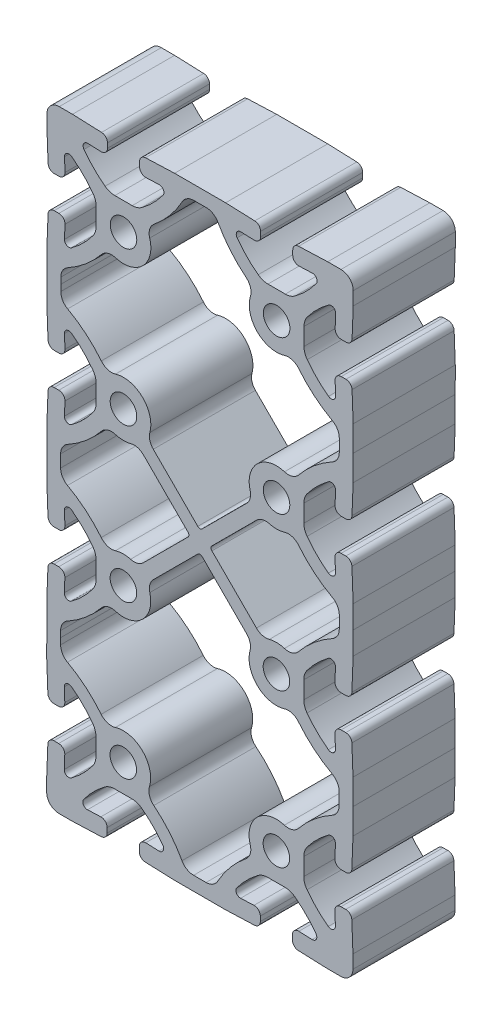
SolidWorks part; units mm, degrees
material "6061 Alloy"
ref_plane "Front" through (0, 0, 0) normal (0, 0, 1) x (1, 0, 0)
ref_plane "Top" through (0, 0, 0) normal (0, 1, 0) x (1, 0, 0)
ref_plane "Right" through (0, 0, 0) normal (1, 0, 0) x (0, 0, -1)
sketch "Sketch1" plane through (0, 0, 0) normal (0, 0, 1) x (1, 0, 0)
  line L0 (29.1885, -14.6975) -> (32.5093, -14.5704)
  line L1 (34.0916, -16.094) -> (34.0911, -17.2633)
  line L2 (32.6254, -18.7854) -> (25.3907, -19.0624)
  line L3 (25.3907, -19.0624) -> (19.0407, -19.0593)
  line L4 (38.0967, -6.8258) -> (35.9379, -6.8248)
  line L5 (19.0407, -19.0593) -> (12.6907, -19.0562)
  line L6 (40.2554, -6.8269) -> (38.0967, -6.8258)
  line L7 (12.6907, -19.0562) -> (5.4563, -18.7721)
  line L8 (3.9921, -17.2486) -> (3.9926, -16.0793)
  line L9 (43.6764, -14.5758) -> (46.9971, -14.7062)
  line L10 (5.5764, -14.5572) -> (8.8971, -14.6876)
  line L11 (42.0921, -17.2672) -> (42.0926, -16.0979)
  line L12 (50.7907, -19.0748) -> (43.5563, -18.7907)
  line L13 (2.1554, -6.8083) -> (-0.0033, -6.8072)
  line L14 (54.0927, -19.0764) -> (50.7907, -19.0748)
  line L15 (-0.0033, -6.8072) -> (-2.1621, -6.8061)
  line L16 (57.1438, -12.7279) -> (57.1422, -16.0299)
  line L17 (56.8668, -5.4932) -> (57.1438, -12.7279)
  line L18 (-8.9115, -14.6789) -> (-5.5907, -14.5517)
  line L19 (54.1754, -4.027) -> (55.3446, -4.0275)
  line L20 (-4.0084, -16.0754) -> (-4.0089, -17.2446)
  line L21 (52.7789, -8.9301) -> (52.6517, -5.6093)
  line L22 (-5.4746, -18.7668) -> (-12.7093, -19.0438)
  line L23 (-12.7093, -19.0438) -> (-16.0113, -19.0422)
  line L24 (44.9072, -0.0219) -> (44.9061, -2.1807)
  line L25 (-19.0578, -15.9927) -> (-19.0562, -12.6907)
  line L26 (44.9082, 2.1368) -> (44.9072, -0.0219)
  line L27 (-19.0562, -12.6907) -> (-18.7721, -5.4563)
  line L28 (-17.2486, -3.9921) -> (-16.0793, -3.9926)
  line L29 (52.6572, 5.5578) -> (52.7876, 8.8785)
  line L30 (-14.5572, -5.5764) -> (-14.6876, -8.8971)
  line L31 (55.3485, 3.9735) -> (54.1793, 3.974)
  line L32 (57.1562, 12.6721) -> (56.8721, 5.4377)
  line L33 (-6.8083, -2.1554) -> (-6.8072, 0.0033)
  line L34 (57.1593, 19.0229) -> (57.1562, 12.6721)
  line L35 (-6.8072, 0.0033) -> (-6.8061, 2.1621)
  line L36 (57.1593, 25.3738) -> (57.1593, 19.0229)
  line L37 (56.8788, 32.6083) -> (57.1593, 25.3738)
  line L38 (54.1866, 34.0733) -> (55.3559, 34.0733)
  line L39 (-14.6789, 8.9115) -> (-14.5517, 5.5907)
  line L40 (52.7925, 29.1694) -> (52.6638, 32.4902)
  line L41 (-16.0754, 4.0084) -> (-17.2446, 4.0089)
  line L42 (-18.7668, 5.4746) -> (-19.0438, 12.7093)
  line L43 (-19.0438, 12.7093) -> (-19.0407, 19.0602)
  line L44 (44.9165, 38.0738) -> (44.9165, 35.915)
  line L45 (-19.0407, 19.0602) -> (-19.0345, 25.411)
  line L46 (44.9165, 40.2325) -> (44.9165, 38.0738)
  line L47 (-19.0345, 25.411) -> (-18.7469, 32.6453)
  line L48 (-17.2226, 34.1087) -> (-16.0533, 34.1076)
  line L49 (52.6638, 43.6573) -> (52.7925, 46.9781)
  line L50 (-14.532, 32.523) -> (-14.664, 29.2024)
  line L51 (55.3559, 42.0743) -> (54.1866, 42.0743)
  line L52 (57.1855, 51.4485) -> (56.8788, 43.5392)
  line L53 (-6.7814, 35.9403) -> (-6.7793, 38.099)
  line L54 (57.1965, 57.1006) -> (57.1855, 51.4485)
  line L55 (-6.7793, 38.099) -> (-6.7772, 40.2578)
  line L56 (57.191, 62.7528) -> (57.1965, 57.1006)
  line L57 (56.892, 70.6624) -> (57.191, 62.7528)
  line L58 (54.2013, 72.1299) -> (55.3706, 72.1288)
  line L59 (-14.6466, 47.011) -> (-14.5211, 43.6901)
  line L60 (52.8024, 67.2275) -> (52.6769, 70.5484)
  line L61 (-16.0455, 42.1086) -> (-17.2148, 42.1097)
  line L62 (-18.7362, 43.5762) -> (-19.0352, 51.4858)
  line L63 (-19.0352, 51.4858) -> (-19.0407, 57.1379)
  line L64 (44.9351, 76.1395) -> (44.933, 73.9807)
  line L65 (-19.0407, 57.1379) -> (-19.0296, 62.79)
  line L66 (44.9372, 78.2983) -> (44.9351, 76.1395)
  line L67 (-19.0296, 62.79) -> (-18.7229, 70.6993)
  line L68 (-17.2001, 72.1643) -> (-16.0308, 72.1643)
  line L69 (52.6878, 81.7155) -> (52.8198, 85.0361)
  line L70 (-14.5079, 70.5812) -> (-14.6367, 67.2605)
  line L71 (55.3784, 80.1298) -> (54.2091, 80.1309)
  line L72 (57.1903, 88.8275) -> (56.9027, 81.5933)
  line L73 (-6.7607, 74.006) -> (-6.7607, 76.1648)
  line L74 (57.1965, 95.1784) -> (57.1903, 88.8275)
  line L75 (-6.7607, 76.1648) -> (-6.7607, 78.3235)
  line L76 (57.1996, 101.5292) -> (57.1965, 95.1784)
  line L77 (56.9226, 108.7639) -> (57.1996, 101.5292)
  line L78 (54.2312, 110.2302) -> (55.4005, 110.2296)
  line L79 (-14.6367, 85.0691) -> (-14.5079, 81.7483)
  line L80 (52.8347, 105.327) -> (52.7076, 108.6479)
  line L81 (-16.0308, 80.1653) -> (-17.2001, 80.1653)
  line L82 (-18.7229, 81.6302) -> (-19.0035, 88.8648)
  line L83 (-19.0035, 88.8648) -> (-19.0035, 95.2156)
  line L84 (44.963, 114.2352) -> (44.962, 112.0764)
  line L85 (-19.0035, 95.2156) -> (-19.0004, 101.5665)
  line L86 (44.9641, 116.394) -> (44.963, 114.2352)
  line L87 (-19.0004, 101.5665) -> (-18.7163, 108.8009)
  line L88 (-17.1927, 110.2651) -> (-16.0234, 110.2645)
  line L89 (52.713, 119.815) -> (52.8434, 123.1357)
  line L90 (-14.5014, 108.6807) -> (-14.6318, 105.36)
  line L91 (55.4044, 118.2306) -> (54.2351, 118.2312)
  line L92 (57.212, 126.9292) -> (56.928, 119.6948)
  line L93 (-6.7524, 112.1017) -> (-6.7514, 114.2605)
  line L94 (57.2136, 130.2312) -> (57.212, 126.9292)
  line L95 (-6.7514, 114.2605) -> (-6.7503, 116.4192)
  line L96 (50.8651, 133.2823) -> (54.1671, 133.2807)
  line L97 (43.6304, 133.0053) -> (50.8651, 133.2823)
  line L98 (-14.6231, 123.1686) -> (-14.4959, 119.8478)
  line L99 (42.1642, 130.3139) -> (42.1648, 131.4832)
  line L100 (-16.0195, 118.2655) -> (-17.1888, 118.2661)
  line L101 (47.0673, 128.9174) -> (43.7465, 128.7903)
  line L102 (-18.711, 119.7318) -> (-18.988, 126.9665)
  line L103 (-18.988, 126.9665) -> (-18.9863, 130.2685)
  line L104 (38.1592, 121.0457) -> (40.3179, 121.0447)
  line L105 (-15.9369, 133.315) -> (-12.6349, 133.3133)
  line L106 (36.0004, 121.0468) -> (38.1592, 121.0457)
  line L107 (-12.6349, 133.3133) -> (-5.4004, 133.0293)
  line L108 (-3.9362, 131.5057) -> (-3.9368, 130.3364)
  line L109 (32.5794, 128.7957) -> (29.2587, 128.9261)
  line L110 (-5.5206, 128.8143) -> (-8.8413, 128.9447)
  line L111 (34.1638, 131.4871) -> (34.1632, 130.3178)
  line L112 (25.4651, 133.2947) -> (32.6996, 133.0107)
  line L113 (-2.0996, 121.0654) -> (0.0592, 121.0643)
  line L114 (19.1151, 133.2978) -> (25.4651, 133.2947)
  line L115 (0.0592, 121.0643) -> (2.2179, 121.0633)
  line L116 (12.7651, 133.3009) -> (19.1151, 133.2978)
  line L117 (5.5304, 133.0239) -> (12.7651, 133.3009)
  line L118 (4.0642, 130.3325) -> (4.0648, 131.5018)
  line L119 (8.9673, 128.936) -> (5.6465, 128.8089)
  line L120 (19.6152, 54.138) -> (30.6889, 43.0561)
  line L121 (7.4532, 43.0675) -> (18.5377, 54.1386)
  line L122 (53.7049, 19.0238) -> (53.7049, 20.5701)
  line L123 (53.7049, 19.0238) -> (53.7041, 17.4774)
  line L124 (-15.5863, 19.0576) -> (-15.5848, 20.604)
  line L125 (-15.5863, 19.0576) -> (-15.587, 17.5113)
  line L126 (19.0424, -15.6049) -> (20.5887, -15.6057)
  line L127 (19.0424, -15.6049) -> (17.496, -15.6042)
  line L128 (19.1135, 129.8434) -> (20.6598, 129.8427)
  line L129 (19.1135, 129.8434) -> (17.5671, 129.8442)
  line L130 (53.7421, 95.1809) -> (53.7429, 96.7273)
  line L131 (53.7421, 95.1809) -> (53.7406, 93.6346)
  line L132 (-15.5491, 95.2148) -> (-15.5483, 96.7611)
  line L133 (-15.5491, 95.2148) -> (-15.5491, 93.6684)
  line L134 (19.6181, 60.1) -> (30.7026, 71.171)
  line L135 (7.4669, 71.1824) -> (18.5406, 60.1005)
  line L136 (53.7451, 58.6323) -> (53.7391, 55.5602)
  line L137 (22.0596, 56.5789) -> (33.1324, 45.4978)
  line L138 (22.0601, 57.6567) -> (33.1438, 68.7269)
  line L139 (5.012, 45.5116) -> (16.0957, 56.5818)
  line L140 (5.0234, 68.7407) -> (16.0963, 57.6596)
  line L141 (-15.5893, 55.6062) -> (-15.5833, 58.6783)
  arc A0 (34.0916, -16.094) -> (32.5093, -14.5704) centre (32.5676, -16.0932) ccw
  arc A1 (28.2492, -12.9315) -> (29.1885, -14.6975) centre (29.146, -13.5873) ccw
  arc A2 (32.6254, -18.7854) -> (34.0911, -17.2633) centre (32.5671, -17.2625) ccw
  arc A3 (33.511, -7.6275) -> (28.2492, -12.9315) centre (48.4243, -27.6843) ccw
  arc A4 (35.9379, -6.8248) -> (33.511, -7.6275) centre (35.9359, -10.8888) ccw
  arc A5 (42.6816, -7.632) -> (40.2554, -6.8269) centre (40.2535, -10.8909) ccw
  arc A6 (3.9921, -17.2486) -> (5.4563, -18.7721) centre (5.5161, -17.2493) ccw
  arc A7 (47.9382, -12.9411) -> (42.6816, -7.632) centre (27.7487, -27.6742) ccw
  arc A8 (46.9971, -14.7062) -> (47.9382, -12.9411) centre (47.0407, -13.596) ccw
  arc A9 (5.5764, -14.5572) -> (3.9926, -16.0793) centre (5.5166, -16.08) ccw
  arc A10 (43.6764, -14.5758) -> (42.0926, -16.0979) centre (43.6166, -16.0986) ccw
  arc A11 (8.8971, -14.6876) -> (9.8382, -12.9225) centre (8.9407, -13.5774) ccw
  arc A12 (9.8382, -12.9225) -> (4.5816, -7.6134) centre (-10.3513, -27.6555) ccw
  arc A13 (42.0921, -17.2672) -> (43.5563, -18.7907) centre (43.6161, -17.2679) ccw
  arc A14 (4.5816, -7.6134) -> (2.1554, -6.8083) centre (2.1535, -10.8723) ccw
  arc A15 (54.0927, -19.0764) -> (57.1422, -16.0299) centre (54.0942, -16.0284) ccw
  arc A16 (-2.1621, -6.8061) -> (-4.589, -7.6089) centre (-2.1641, -10.8701) ccw
  arc A17 (-4.589, -7.6089) -> (-9.8508, -12.9129) centre (10.3243, -27.6656) ccw
  arc A18 (-9.8508, -12.9129) -> (-8.9115, -14.6789) centre (-8.954, -13.5687) ccw
  arc A19 (56.8668, -5.4932) -> (55.3446, -4.0275) centre (55.3439, -5.5515) ccw
  arc A20 (-4.0084, -16.0754) -> (-5.5907, -14.5517) centre (-5.5324, -16.0746) ccw
  arc A21 (54.1754, -4.027) -> (52.6517, -5.6093) centre (54.1746, -5.551) ccw
  arc A22 (-5.4746, -18.7668) -> (-4.0089, -17.2446) centre (-5.5329, -17.2439) ccw
  arc A23 (51.0129, -9.8695) -> (52.7789, -8.9301) centre (51.6687, -8.9726) ccw
  arc A24 (45.7089, -4.6076) -> (51.0129, -9.8695) centre (65.7656, 10.3057) ccw
  arc A25 (44.9061, -2.1807) -> (45.7089, -4.6076) centre (48.9701, -2.1827) ccw
  arc A26 (-19.0578, -15.9927) -> (-16.0113, -19.0422) centre (-16.0098, -15.9942) ccw
  arc A27 (45.7134, 4.5629) -> (44.9082, 2.1368) centre (48.9722, 2.1348) ccw
  arc A28 (-17.2486, -3.9921) -> (-18.7721, -5.4563) centre (-17.2493, -5.5161) ccw
  arc A29 (51.0225, 9.8196) -> (45.7134, 4.5629) centre (65.7555, -10.3699) ccw
  arc A30 (52.7876, 8.8785) -> (51.0225, 9.8196) centre (51.6774, 8.9221) ccw
  arc A31 (-14.5572, -5.5764) -> (-16.0793, -3.9926) centre (-16.08, -5.5166) ccw
  arc A32 (52.6572, 5.5578) -> (54.1793, 3.974) centre (54.18, 5.498) ccw
  arc A33 (-14.6876, -8.8971) -> (-12.9225, -9.8382) centre (-13.5774, -8.9407) ccw
  arc A34 (-12.9225, -9.8382) -> (-7.6134, -4.5816) centre (-27.6555, 10.3513) ccw
  arc A35 (55.3485, 3.9735) -> (56.8721, 5.4377) centre (55.3493, 5.4975) ccw
  arc A36 (-7.6134, -4.5816) -> (-6.8083, -2.1554) centre (-10.8723, -2.1535) ccw
  arc A37 (-6.8061, 2.1621) -> (-7.6089, 4.589) centre (-10.8701, 2.1641) ccw
  arc A38 (-7.6089, 4.589) -> (-12.9129, 9.8508) centre (-27.6656, -10.3243) ccw
  arc A39 (56.8788, 32.6083) -> (55.3559, 34.0733) centre (55.3559, 32.5493) ccw
  arc A40 (-12.9129, 9.8508) -> (-14.6789, 8.9115) centre (-13.5687, 8.954) ccw
  arc A41 (54.1866, 34.0733) -> (52.6638, 32.4902) centre (54.1866, 32.5493) ccw
  arc A42 (-16.0754, 4.0084) -> (-14.5517, 5.5907) centre (-16.0746, 5.5324) ccw
  arc A43 (51.027, 28.2292) -> (52.7925, 29.1694) centre (51.6823, 29.1264) ccw
  arc A44 (-18.7668, 5.4746) -> (-17.2446, 4.0089) centre (-17.2439, 5.5329) ccw
  arc A45 (45.7204, 33.4885) -> (51.027, 28.2292) centre (65.7699, 48.4116) ccw
  arc A46 (44.9165, 35.915) -> (45.7204, 33.4885) centre (48.9805, 35.915) ccw
  arc A47 (45.7204, 42.659) -> (44.9165, 40.2325) centre (48.9805, 40.2325) ccw
  arc A48 (-17.2226, 34.1087) -> (-18.7469, 32.6453) centre (-17.2241, 32.5847) ccw
  arc A49 (51.027, 47.9183) -> (45.7204, 42.659) centre (65.7699, 27.736) ccw
  arc A50 (52.7925, 46.9781) -> (51.027, 47.9183) centre (51.6823, 47.0211) ccw
  arc A51 (-14.532, 32.523) -> (-16.0533, 34.1076) centre (-16.0548, 32.5836) ccw
  arc A52 (52.6638, 43.6573) -> (54.1866, 42.0743) centre (54.1866, 43.5983) ccw
  arc A53 (-14.664, 29.2024) -> (-12.8994, 28.2605) centre (-13.5539, 29.1583) ccw
  arc A54 (-12.8994, 28.2605) -> (-7.5877, 33.5145) centre (-27.6226, 48.4572) ccw
  arc A55 (55.3559, 42.0743) -> (56.8788, 43.5392) centre (55.3559, 43.5983) ccw
  arc A56 (-7.5877, 33.5145) -> (-6.7814, 35.9403) centre (-10.8454, 35.9442) ccw
  arc A57 (-6.7772, 40.2578) -> (-7.5787, 42.6851) centre (-10.8412, 40.2618) ccw
  arc A58 (-7.5787, 42.6851) -> (-12.8801, 47.9495) centre (-27.6428, 27.7816) ccw
  arc A59 (56.892, 70.6624) -> (55.3706, 72.1288) centre (55.3691, 70.6048) ccw
  arc A60 (-12.8801, 47.9495) -> (-14.6466, 47.011) centre (-13.5364, 47.053) ccw
  arc A61 (54.2013, 72.1299) -> (52.6769, 70.5484) centre (54.1998, 70.6059) ccw
  arc A62 (-16.0455, 42.1086) -> (-14.5211, 43.6901) centre (-16.044, 43.6326) ccw
  arc A63 (51.036, 66.289) -> (52.8024, 67.2275) centre (51.6922, 67.1855) ccw
  arc A64 (-18.7362, 43.5762) -> (-17.2148, 42.1097) centre (-17.2133, 43.6337) ccw
  arc A65 (45.7345, 71.5534) -> (51.036, 66.289) centre (65.7986, 86.4569) ccw
  arc A66 (44.933, 73.9807) -> (45.7345, 71.5534) centre (48.997, 73.9768) ccw
  arc A67 (45.7435, 80.724) -> (44.9372, 78.2983) centre (49.0012, 78.2943) ccw
  arc A68 (-17.2001, 72.1643) -> (-18.7229, 70.6993) centre (-17.2001, 70.6403) ccw
  arc A69 (51.0552, 85.9781) -> (45.7435, 80.724) centre (65.7784, 65.7813) ccw
  arc A70 (52.8198, 85.0361) -> (51.0552, 85.9781) centre (51.7097, 85.0803) ccw
  arc A71 (-14.5079, 70.5812) -> (-16.0308, 72.1643) centre (-16.0308, 70.6403) ccw
  arc A72 (52.6878, 81.7155) -> (54.2091, 80.1309) centre (54.2106, 81.6549) ccw
  arc A73 (-14.6367, 67.2605) -> (-12.8712, 66.3202) centre (-13.5265, 67.2174) ccw
  arc A74 (-12.8712, 66.3202) -> (-7.5646, 71.5795) centre (-27.6141, 86.5026) ccw
  arc A75 (55.3784, 80.1298) -> (56.9027, 81.5933) centre (55.3799, 81.6538) ccw
  arc A76 (-7.5646, 71.5795) -> (-6.7607, 74.006) centre (-10.8247, 74.006) ccw
  arc A77 (-6.7607, 78.3235) -> (-7.5646, 80.7501) centre (-10.8247, 78.3235) ccw
  arc A78 (-7.5646, 80.7501) -> (-12.8712, 86.0093) centre (-27.6141, 65.827) ccw
  arc A79 (56.9226, 108.7639) -> (55.4005, 110.2296) centre (55.3997, 108.7056) ccw
  arc A80 (-12.8712, 86.0093) -> (-14.6367, 85.0691) centre (-13.5265, 85.1121) ccw
  arc A81 (54.2312, 110.2302) -> (52.7076, 108.6479) centre (54.2304, 108.7062) ccw
  arc A82 (-16.0308, 80.1653) -> (-14.5079, 81.7483) centre (-16.0308, 81.6893) ccw
  arc A83 (51.0687, 104.3877) -> (52.8347, 105.327) centre (51.7245, 105.2845) ccw
  arc A84 (-18.7229, 81.6302) -> (-17.2001, 80.1653) centre (-17.2001, 81.6893) ccw
  arc A85 (45.7647, 109.6495) -> (51.0687, 104.3877) centre (65.8215, 124.5628) ccw
  arc A86 (44.962, 112.0764) -> (45.7647, 109.6495) centre (49.026, 112.0744) ccw
  arc A87 (45.7692, 118.8201) -> (44.9641, 116.394) centre (49.0281, 116.392) ccw
  arc A88 (-17.1927, 110.2651) -> (-18.7163, 108.8009) centre (-17.1935, 108.7411) ccw
  arc A89 (51.0783, 124.0767) -> (45.7692, 118.8201) centre (65.8114, 103.8872) ccw
  arc A90 (52.8434, 123.1357) -> (51.0783, 124.0767) centre (51.7332, 123.1793) ccw
  arc A91 (-14.5014, 108.6807) -> (-16.0234, 110.2645) centre (-16.0242, 108.7405) ccw
  arc A92 (52.713, 119.815) -> (54.2351, 118.2312) centre (54.2358, 119.7552) ccw
  arc A93 (-14.6318, 105.36) -> (-12.8667, 104.4189) centre (-13.5216, 105.3164) ccw
  arc A94 (-12.8667, 104.4189) -> (-7.5575, 109.6756) centre (-27.5997, 124.6085) ccw
  arc A95 (55.4044, 118.2306) -> (56.928, 119.6948) centre (55.4051, 119.7546) ccw
  arc A96 (-7.5575, 109.6756) -> (-6.7524, 112.1017) centre (-10.8164, 112.1037) ccw
  arc A97 (57.2136, 130.2312) -> (54.1671, 133.2807) centre (54.1656, 130.2327) ccw
  arc A98 (-6.7503, 116.4192) -> (-7.553, 118.8461) centre (-10.8143, 116.4212) ccw
  arc A99 (-7.553, 118.8461) -> (-12.857, 124.108) centre (-27.6098, 103.9329) ccw
  arc A100 (-12.857, 124.108) -> (-14.6231, 123.1686) centre (-13.5128, 123.2111) ccw
  arc A101 (43.6304, 133.0053) -> (42.1648, 131.4832) centre (43.6888, 131.4824) ccw
  arc A102 (-16.0195, 118.2655) -> (-14.4959, 119.8478) centre (-16.0188, 119.7895) ccw
  arc A103 (42.1642, 130.3139) -> (43.7465, 128.7903) centre (43.6882, 130.3131) ccw
  arc A104 (-18.711, 119.7318) -> (-17.1888, 118.2661) centre (-17.1881, 119.7901) ccw
  arc A105 (48.0067, 127.1514) -> (47.0673, 128.9174) centre (47.1098, 127.8072) ccw
  arc A106 (42.7448, 121.8474) -> (48.0067, 127.1514) centre (27.8315, 141.9042) ccw
  arc A107 (40.3179, 121.0447) -> (42.7448, 121.8474) centre (40.3199, 125.1087) ccw
  arc A108 (-15.9369, 133.315) -> (-18.9863, 130.2685) centre (-15.9383, 130.267) ccw
  arc A109 (33.5743, 121.8519) -> (36.0004, 121.0468) centre (36.0024, 125.1108) ccw
  arc A110 (-3.9362, 131.5057) -> (-5.4004, 133.0293) centre (-5.4602, 131.5064) ccw
  arc A111 (28.3176, 127.161) -> (33.5743, 121.8519) centre (48.5071, 141.8941) ccw
  arc A112 (29.2587, 128.9261) -> (28.3176, 127.161) centre (29.2151, 127.8159) ccw
  arc A113 (-5.5206, 128.8143) -> (-3.9368, 130.3364) centre (-5.4608, 130.3372) ccw
  arc A114 (32.5794, 128.7957) -> (34.1632, 130.3178) centre (32.6392, 130.3185) ccw
  arc A115 (-8.8413, 128.9447) -> (-9.7824, 127.1796) centre (-8.8849, 127.8346) ccw
  arc A116 (-9.7824, 127.1796) -> (-4.5257, 121.8705) centre (10.4071, 141.9127) ccw
  arc A117 (34.1638, 131.4871) -> (32.6996, 133.0107) centre (32.6398, 131.4878) ccw
  arc A118 (-4.5257, 121.8705) -> (-2.0996, 121.0654) centre (-2.0976, 125.1294) ccw
  arc A119 (2.2179, 121.0633) -> (4.6448, 121.866) centre (2.2199, 125.1273) ccw
  arc A120 (4.6448, 121.866) -> (9.9067, 127.17) centre (-10.2685, 141.9228) ccw
  arc A121 (5.5304, 133.0239) -> (4.0648, 131.5018) centre (5.5888, 131.501) ccw
  arc A122 (9.9067, 127.17) -> (8.9673, 128.936) centre (9.0098, 127.8258) ccw
  arc A123 (4.0642, 130.3325) -> (5.6465, 128.8089) centre (5.5882, 130.3318) ccw
  arc A124 (19.6152, 54.138) -> (18.5377, 54.1386) centre (19.0762, 53.5994) ccw
  arc A125 (31.5398, 39.8571) -> (30.6889, 43.0561) centre (28.3532, 40.7221) ccw
  arc A126 (31.5398, 39.8571) -> (31.3021, 38.0738) centre (38.1093, 38.0738) ccw
  arc A127 (7.4532, 43.0675) -> (6.5991, 39.8693) centre (9.7866, 40.7312) ccw
  arc A128 (31.3021, 38.0738) -> (33.2959, 33.2603) centre (38.1093, 38.0738) ccw
  arc A129 (6.8351, 38.0857) -> (6.5991, 39.8693) centre (0.0279, 38.0924) ccw
  arc A130 (33.2959, 33.2603) -> (38.1093, 31.2666) centre (38.1093, 38.0738) ccw
  arc A131 (4.8366, 33.2742) -> (6.8351, 38.0857) centre (0.0279, 38.0924) ccw
  arc A132 (38.1093, 31.2666) -> (40.0914, 31.5615) centre (38.1093, 38.0738) ccw
  arc A133 (0.0213, 31.2852) -> (4.8366, 33.2742) centre (0.0279, 38.0924) ccw
  arc A134 (43.6193, 30.4802) -> (40.0914, 31.5615) centre (41.0529, 28.4026) ccw
  arc A135 (-1.9605, 31.5821) -> (0.0213, 31.2852) centre (0.0279, 38.0924) ccw
  arc A136 (43.6193, 30.4802) -> (51.9985, 23.461) centre (65.7699, 48.4116) ccw
  arc A137 (-1.9605, 31.5821) -> (-5.4895, 30.5042) centre (-2.9251, 28.4241) ccw
  arc A138 (53.7049, 20.5701) -> (51.9985, 23.461) centre (50.4029, 20.5701) ccw
  arc A139 (-13.8756, 23.4932) -> (-5.4895, 30.5042) centre (-27.6226, 48.4572) ccw
  arc A140 (-13.8756, 23.4932) -> (-15.5848, 20.604) centre (-12.2828, 20.6007) ccw
  arc A141 (51.9963, 14.5874) -> (53.7041, 17.4774) centre (50.4021, 17.479) ccw
  arc A142 (51.9963, 14.5874) -> (43.6137, 7.5722) centre (65.7555, -10.3699) ccw
  arc A143 (-15.587, 17.5113) -> (-13.8821, 14.6195) centre (-12.285, 17.5097) ccw
  arc A144 (40.0853, 6.4927) -> (43.6137, 7.5722) centre (41.0483, 9.6511) ccw
  arc A145 (-5.5063, 7.5962) -> (-13.8821, 14.6195) centre (-27.6656, -10.3243) ccw
  arc A146 (40.0853, 6.4927) -> (38.1033, 6.7886) centre (38.1, -0.0186) ccw
  arc A147 (-5.5063, 7.5962) -> (-1.9789, 6.5132) centre (-2.9388, 9.6726) ccw
  arc A148 (38.1033, 6.7886) -> (33.2889, 4.7972) centre (38.1, -0.0186) ccw
  arc A149 (0.0033, 6.8072) -> (-1.9789, 6.5132) centre (0, 0) ccw
  arc A150 (33.2889, 4.7972) -> (31.2928, -0.0153) centre (38.1, -0.0186) ccw
  arc A151 (4.8158, 4.8111) -> (0.0033, 6.8072) centre (0, 0) ccw
  arc A152 (31.2928, -0.0153) -> (31.5868, -1.9975) centre (38.1, -0.0186) ccw
  arc A153 (6.8072, -0.0033) -> (4.8158, 4.8111) centre (0, 0) ccw
  arc A154 (30.5037, -5.5249) -> (31.5868, -1.9975) centre (28.4274, -2.9574) ccw
  arc A155 (6.5113, -1.9853) -> (6.8072, -0.0033) centre (0, 0) ccw
  arc A156 (30.5037, -5.5249) -> (23.4804, -13.9007) centre (48.4243, -27.6843) ccw
  arc A157 (6.5113, -1.9853) -> (7.5909, -5.5137) centre (9.6697, -2.9483) ccw
  arc A158 (20.5887, -15.6057) -> (23.4804, -13.9007) centre (20.5903, -12.3037) ccw
  arc A159 (14.606, -13.8964) -> (7.5909, -5.5137) centre (-10.3513, -27.6555) ccw
  arc A160 (14.606, -13.8964) -> (17.496, -15.6042) centre (17.4976, -12.3022) ccw
  arc A161 (0.0247, 34.7904) -> (2.3605, 35.7552) centre (0.0279, 38.0924) ccw
  arc A162 (2.3605, 35.7552) -> (3.3299, 38.0891) centre (0.0279, 38.0924) ccw
  arc A163 (-2.3092, 35.7598) -> (0.0247, 34.7904) centre (0.0279, 38.0924) ccw
  arc A164 (3.3299, 38.0891) -> (2.3651, 40.425) centre (0.0279, 38.0924) ccw
  arc A165 (-3.2741, 38.0956) -> (-2.3092, 35.7598) centre (0.0279, 38.0924) ccw
  arc A166 (2.3651, 40.425) -> (0.0311, 41.3944) centre (0.0279, 38.0924) ccw
  arc A167 (-2.3047, 40.4295) -> (-3.2741, 38.0956) centre (0.0279, 38.0924) ccw
  arc A168 (0.0311, 41.3944) -> (-2.3047, 40.4295) centre (0.0279, 38.0924) ccw
  arc A169 (38.1093, 34.7718) -> (40.4442, 35.7389) centre (38.1093, 38.0738) ccw
  arc A170 (40.4442, 35.7389) -> (41.4113, 38.0738) centre (38.1093, 38.0738) ccw
  arc A171 (35.7744, 35.7389) -> (38.1093, 34.7718) centre (38.1093, 38.0738) ccw
  arc A172 (41.4113, 38.0738) -> (40.4442, 40.4086) centre (38.1093, 38.0738) ccw
  arc A173 (34.8073, 38.0738) -> (35.7744, 35.7389) centre (38.1093, 38.0738) ccw
  arc A174 (40.4442, 40.4086) -> (38.1093, 41.3758) centre (38.1093, 38.0738) ccw
  arc A175 (35.7744, 40.4086) -> (34.8073, 38.0738) centre (38.1093, 38.0738) ccw
  arc A176 (38.1093, 41.3758) -> (35.7744, 40.4086) centre (38.1093, 38.0738) ccw
  arc A177 (-2.336, -2.3337) -> (-0.0016, -3.302) centre (0, 0) ccw
  arc A178 (-0.0016, -3.302) -> (2.3337, -2.336) centre (0, 0) ccw
  arc A179 (-3.302, 0.0016) -> (-2.336, -2.3337) centre (0, 0) ccw
  arc A180 (2.3337, -2.336) -> (3.302, -0.0016) centre (0, 0) ccw
  arc A181 (-2.3337, 2.336) -> (-3.302, 0.0016) centre (0, 0) ccw
  arc A182 (3.302, -0.0016) -> (2.336, 2.3337) centre (0, 0) ccw
  arc A183 (0.0016, 3.302) -> (-2.3337, 2.336) centre (0, 0) ccw
  arc A184 (2.336, 2.3337) -> (0.0016, 3.302) centre (0, 0) ccw
  arc A185 (38.0984, -3.3206) -> (40.4337, -2.3546) centre (38.1, -0.0186) ccw
  arc A186 (40.4337, -2.3546) -> (41.402, -0.0202) centre (38.1, -0.0186) ccw
  arc A187 (35.764, -2.3523) -> (38.0984, -3.3206) centre (38.1, -0.0186) ccw
  arc A188 (41.402, -0.0202) -> (40.436, 2.3151) centre (38.1, -0.0186) ccw
  arc A189 (34.798, -0.017) -> (35.764, -2.3523) centre (38.1, -0.0186) ccw
  arc A190 (40.436, 2.3151) -> (38.1016, 3.2834) centre (38.1, -0.0186) ccw
  arc A191 (35.7663, 2.3174) -> (34.798, -0.017) centre (38.1, -0.0186) ccw
  arc A192 (38.1016, 3.2834) -> (35.7663, 2.3174) centre (38.1, -0.0186) ccw
  arc A193 (23.5499, 128.1349) -> (30.565, 119.7523) centre (48.5071, 141.8941) ccw
  arc A194 (23.5499, 128.1349) -> (20.6598, 129.8427) centre (20.6582, 126.5407) ccw
  arc A195 (31.6446, 116.2238) -> (30.565, 119.7523) centre (28.4861, 117.1868) ccw
  arc A196 (31.6446, 116.2238) -> (31.3486, 114.2419) centre (38.1558, 114.2385) ccw
  arc A197 (31.3486, 114.2419) -> (33.3401, 109.4275) centre (38.1558, 114.2385) ccw
  arc A198 (17.5671, 129.8442) -> (14.6754, 128.1392) centre (17.5655, 126.5422) ccw
  arc A199 (33.3401, 109.4275) -> (38.1525, 107.4313) centre (38.1558, 114.2385) ccw
  arc A200 (7.6521, 119.7635) -> (14.6754, 128.1392) centre (-10.2685, 141.9228) ccw
  arc A201 (38.1525, 107.4313) -> (40.1347, 107.7253) centre (38.1558, 114.2385) ccw
  arc A202 (7.6521, 119.7635) -> (6.569, 116.2361) centre (9.7284, 117.196) ccw
  arc A203 (43.6621, 106.6423) -> (40.1347, 107.7253) centre (41.0947, 104.5659) ccw
  arc A204 (6.863, 114.2538) -> (6.569, 116.2361) centre (0.0558, 114.2571) ccw
  arc A205 (43.6621, 106.6423) -> (52.0379, 99.619) centre (65.8215, 124.5628) ccw
  arc A206 (4.8669, 109.4414) -> (6.863, 114.2538) centre (0.0558, 114.2571) ccw
  arc A207 (53.7429, 96.7273) -> (52.0379, 99.619) centre (50.4409, 96.7289) ccw
  arc A208 (0.0525, 107.4499) -> (4.8669, 109.4414) centre (0.0558, 114.2571) ccw
  arc A209 (-1.9294, 107.7459) -> (0.0525, 107.4499) centre (0.0558, 114.2571) ccw
  arc A210 (-1.9294, 107.7459) -> (-5.4579, 106.6663) centre (-2.8924, 104.5874) ccw
  arc A211 (52.0314, 90.7453) -> (53.7406, 93.6346) centre (50.4386, 93.6378) ccw
  arc A212 (-13.8405, 99.6512) -> (-5.4579, 106.6663) centre (-27.5997, 124.6085) ccw
  arc A213 (52.0314, 90.7453) -> (43.6453, 83.7343) centre (65.7784, 65.7813) ccw
  arc A214 (-13.8405, 99.6512) -> (-15.5483, 96.7611) centre (-12.2463, 96.7595) ccw
  arc A215 (40.1164, 82.6565) -> (43.6453, 83.7343) centre (41.0809, 85.8144) ccw
  arc A216 (40.1164, 82.6565) -> (38.1346, 82.9534) centre (38.1279, 76.1462) ccw
  arc A217 (38.1346, 82.9534) -> (33.3192, 80.9643) centre (38.1279, 76.1462) ccw
  arc A218 (-15.5491, 93.6684) -> (-13.8427, 90.7775) centre (-12.2471, 93.6684) ccw
  arc A219 (33.3192, 80.9643) -> (31.3207, 76.1528) centre (38.1279, 76.1462) ccw
  arc A220 (-5.4635, 83.7583) -> (-13.8427, 90.7775) centre (-27.6141, 65.827) ccw
  arc A221 (31.3207, 76.1528) -> (31.5567, 74.3693) centre (38.1279, 76.1462) ccw
  arc A222 (-5.4635, 83.7583) -> (-1.9356, 82.677) centre (-2.897, 85.8359) ccw
  arc A223 (30.7026, 71.171) -> (31.5567, 74.3693) centre (28.3692, 73.5073) ccw
  arc A224 (0.0465, 82.972) -> (-1.9356, 82.677) centre (0.0465, 76.1648) ccw
  arc A225 (4.8599, 80.9782) -> (0.0465, 82.972) centre (0.0465, 76.1648) ccw
  arc A226 (18.5406, 60.1005) -> (19.6181, 60.1) centre (19.0796, 60.6391) ccw
  arc A227 (6.8537, 76.1648) -> (4.8599, 80.9782) centre (0.0465, 76.1648) ccw
  arc A228 (6.616, 74.3814) -> (6.8537, 76.1648) centre (0.0465, 76.1648) ccw
  arc A229 (6.616, 74.3814) -> (7.4669, 71.1824) centre (9.8027, 73.5164) ccw
  arc A230 (0.0542, 110.9551) -> (2.3896, 111.9211) centre (0.0558, 114.2571) ccw
  arc A231 (2.3896, 111.9211) -> (3.3578, 114.2555) centre (0.0558, 114.2571) ccw
  arc A232 (-2.2802, 111.9234) -> (0.0542, 110.9551) centre (0.0558, 114.2571) ccw
  arc A233 (3.3578, 114.2555) -> (2.3918, 116.5909) centre (0.0558, 114.2571) ccw
  arc A234 (-3.2462, 114.2588) -> (-2.2802, 111.9234) centre (0.0558, 114.2571) ccw
  arc A235 (2.3918, 116.5909) -> (0.0574, 117.5591) centre (0.0558, 114.2571) ccw
  arc A236 (-2.2779, 116.5932) -> (-3.2462, 114.2588) centre (0.0558, 114.2571) ccw
  arc A237 (0.0574, 117.5591) -> (-2.2779, 116.5932) centre (0.0558, 114.2571) ccw
  arc A238 (38.1542, 110.9365) -> (40.4896, 111.9025) centre (38.1558, 114.2385) ccw
  arc A239 (40.4896, 111.9025) -> (41.4578, 114.2369) centre (38.1558, 114.2385) ccw
  arc A240 (35.8198, 111.9048) -> (38.1542, 110.9365) centre (38.1558, 114.2385) ccw
  arc A241 (41.4578, 114.2369) -> (40.4918, 116.5723) centre (38.1558, 114.2385) ccw
  arc A242 (34.8538, 114.2401) -> (35.8198, 111.9048) centre (38.1558, 114.2385) ccw
  arc A243 (40.4918, 116.5723) -> (38.1574, 117.5405) centre (38.1558, 114.2385) ccw
  arc A244 (35.8221, 116.5745) -> (34.8538, 114.2401) centre (38.1558, 114.2385) ccw
  arc A245 (38.1574, 117.5405) -> (35.8221, 116.5745) centre (38.1558, 114.2385) ccw
  arc A246 (40.0983, 44.5839) -> (43.6264, 45.6603) centre (41.0631, 47.7418) ccw
  arc A247 (52.0271, 52.6727) -> (43.6264, 45.6603) centre (65.7497, 27.6952) ccw
  arc A248 (40.0983, 44.5839) -> (36.3309, 44.6445) centre (38.1093, 38.0738) ccw
  arc A249 (52.0271, 52.6727) -> (53.7391, 55.5602) centre (50.4371, 55.5666) ccw
  arc A250 (33.1324, 45.4978) -> (36.3309, 44.6445) centre (35.4682, 47.8319) ccw
  arc A251 (53.7451, 58.6323) -> (52.0354, 61.5315) centre (50.4431, 58.6388) ccw
  arc A252 (22.0601, 57.6567) -> (22.0596, 56.5789) centre (22.5986, 57.1175) ccw
  arc A253 (43.6376, 68.5542) -> (52.0354, 61.5315) centre (65.7784, 86.4977) ccw
  arc A254 (43.6376, 68.5542) -> (40.1105, 69.6341) centre (41.0723, 66.4752) ccw
  arc A255 (36.343, 69.5771) -> (33.1438, 68.7269) centre (35.4772, 66.3907) ccw
  arc A256 (36.343, 69.5771) -> (40.1105, 69.6341) centre (38.1279, 76.1462) ccw
  arc A257 (0.0465, 72.8628) -> (2.3814, 73.8299) centre (0.0465, 76.1648) ccw
  arc A258 (2.3814, 73.8299) -> (3.3485, 76.1648) centre (0.0465, 76.1648) ccw
  arc A259 (-2.2883, 73.8299) -> (0.0465, 72.8628) centre (0.0465, 76.1648) ccw
  arc A260 (3.3485, 76.1648) -> (2.3814, 78.4996) centre (0.0465, 76.1648) ccw
  arc A261 (-3.2555, 76.1648) -> (-2.2883, 73.8299) centre (0.0465, 76.1648) ccw
  arc A262 (2.3814, 78.4996) -> (0.0465, 79.4668) centre (0.0465, 76.1648) ccw
  arc A263 (-2.2883, 78.4996) -> (-3.2555, 76.1648) centre (0.0465, 76.1648) ccw
  arc A264 (0.0465, 79.4668) -> (-2.2883, 78.4996) centre (0.0465, 76.1648) ccw
  arc A265 (1.8128, 44.6614) -> (5.012, 45.5116) centre (2.6786, 47.8479) ccw
  arc A266 (1.8128, 44.6614) -> (-1.9547, 44.6044) centre (0.0279, 38.0924) ccw
  arc A267 (16.0957, 56.5818) -> (16.0963, 57.6596) centre (15.5572, 57.121) ccw
  arc A268 (-5.4818, 45.6843) -> (-1.9547, 44.6044) centre (-2.9164, 47.7633) ccw
  arc A269 (-5.4818, 45.6843) -> (-13.8796, 52.7071) centre (-27.6226, 27.7408) ccw
  arc A270 (5.0234, 68.7407) -> (1.825, 69.594) centre (2.6877, 66.4067) ccw
  arc A271 (-15.5893, 55.6062) -> (-13.8796, 52.7071) centre (-12.2873, 55.5998) ccw
  arc A272 (-1.9425, 69.6546) -> (1.825, 69.594) centre (0.0465, 76.1648) ccw
  arc A273 (-1.9425, 69.6546) -> (-5.4706, 68.5782) centre (-2.9073, 66.4967) ccw
  arc A274 (-13.8712, 61.5659) -> (-15.5833, 58.6783) centre (-12.2813, 58.6719) ccw
  arc A275 (-13.8712, 61.5659) -> (-5.4706, 68.5782) centre (-27.5938, 86.5433) ccw
  arc A276 (38.1247, 72.8442) -> (40.4605, 73.809) centre (38.1279, 76.1462) ccw
  arc A277 (40.4605, 73.809) -> (41.4299, 76.1429) centre (38.1279, 76.1462) ccw
  arc A278 (35.7908, 73.8136) -> (38.1247, 72.8442) centre (38.1279, 76.1462) ccw
  arc A279 (41.4299, 76.1429) -> (40.4651, 78.4787) centre (38.1279, 76.1462) ccw
  arc A280 (34.8259, 76.1494) -> (35.7908, 73.8136) centre (38.1279, 76.1462) ccw
  arc A281 (40.4651, 78.4787) -> (38.1311, 79.4482) centre (38.1279, 76.1462) ccw
  arc A282 (35.7953, 78.4833) -> (34.8259, 76.1494) centre (38.1279, 76.1462) ccw
  arc A283 (38.1311, 79.4482) -> (35.7953, 78.4833) centre (38.1279, 76.1462) ccw
extrude "Extrude1" add sketch "Sketch1" along normal blind 25.4
